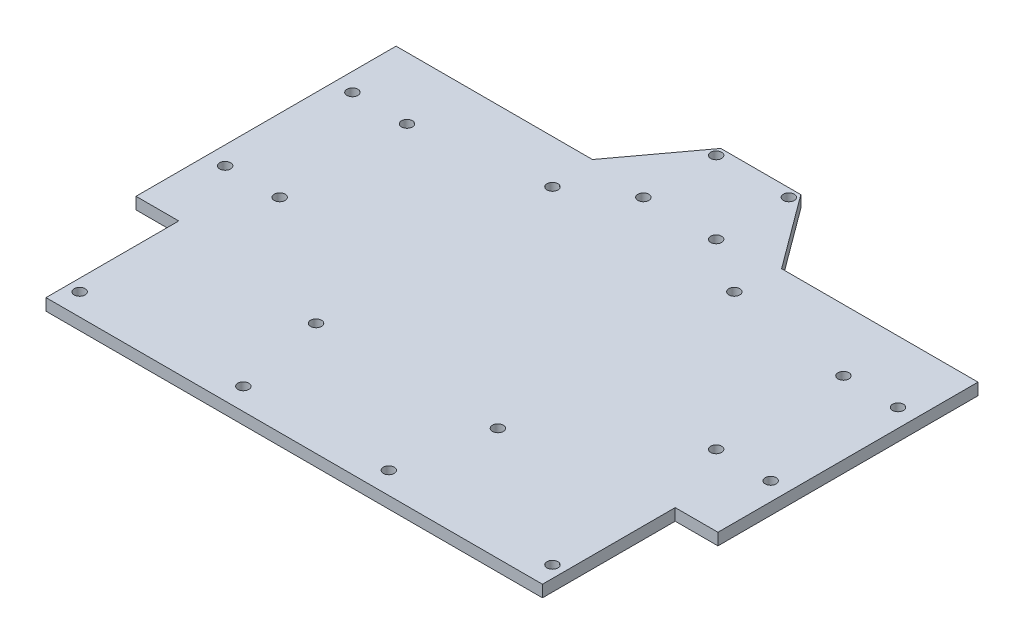
SolidWorks part; units mm, degrees
ref_plane "Front Plane" through (0, 0, 0) normal (0, 0, 1) x (1, 0, 0)
ref_plane "Top Plane" through (0, 0, 0) normal (0, 1, 0) x (1, 0, 0)
ref_plane "Right Plane" through (0, 0, 0) normal (1, 0, 0) x (0, 0, -1)
sketch "Sketch1" plane through (0, 0, 0) normal (0, 1, 0) x (1, 0, 0)
  line L1 (-11, 56.0362) -> (11, 56.0362)
  line L2 (-80, 35.75) -> (-80, -35.75)
  line L3 (-68.25, -72.25) -> (68.25, -72.25)
  line L4 (80, 35.75) -> (80, -35.75)
  line L5 (-80, -35.75) -> (-68.25, -35.75)
  line L6 (-68.25, -72.25) -> (-68.25, -35.75)
  line L7 (68.25, -72.25) -> (68.25, -35.75)
  line L8 (68.25, -35.75) -> (80, -35.75)
  line L9 (-80, 35.75) -> (-26, 35.75)
  line L10 (-26, 35.75) -> (-11, 56.0362)
  line L11 (11, 56.0362) -> (26, 35.75)
  line L12 (26, 35.75) -> (80, 35.75)
  circle A13 centre (-10, 33.75) radius 1.5025
  circle A17 centre (10, 33.75) radius 1.5025
  circle A134 centre (-10, 53.75) radius 1.5025
  circle A138 centre (10, 53.75) radius 1.5025
  circle A195 centre (-25, 23.75) radius 1.5025
  circle A205 centre (25, 23.75) radius 1.5025
  circle A218 centre (-60, 18.75) radius 1.5025
  circle A242 centre (60, 18.75) radius 1.5025
  circle A245 centre (75, 18.75) radius 1.5025
  circle A428 centre (-60, -16.25) radius 1.5025
  circle A452 centre (60, -16.25) radius 1.5025
  circle A455 centre (75, -16.25) radius 1.5025
  circle A585 centre (-25, -41.25) radius 1.5025
  circle A595 centre (25, -41.25) radius 1.5025
  circle A727 centre (-65, -66.25) radius 1.5025
  circle A736 centre (-20, -66.25) radius 1.5025
  circle A744 centre (20, -66.25) radius 1.5025
  circle A753 centre (65, -66.25) radius 1.5025
  circle A757 centre (-75, 18.75) radius 1.5025
  circle A764 centre (-75, -16.25) radius 1.5025
  dimension "D12" = 15
  dimension "D13" = 17
  dimension "D14" = 15
  dimension "D18" = 5
  dimension "D19" = 5
  dimension "D23" = 45
  dimension "D39" = 35
  dimension "D1" = 108
  dimension "D2" = 52
  dimension "D3" = 22
  dimension "D4" = 71.5
  dimension "D5" = 36.5
  dimension "D6" = 136.5
  dimension "D7" = 15
  dimension "D8" = 160
  dimension "D9" = 54
  dimension "D10" = 11.75
  dimension "D11" = 36.5
  dimension "D17" = 17
  dimension "D22" = 19.5
  dimension "D15" = 19.5
  dimension "D16" = 15
  dimension "D20" = 15
  dimension "D21" = 5
  dimension "D24" = 3.25
  dimension "D25" = 43.25
  dimension "D26" = 43.25
  dimension "D27" = 45
  dimension "D28" = 3.25
  dimension "D29" = 25
  dimension "D30" = 25
  dimension "D31" = 50
  dimension "D32" = 12
  dimension "D33" = 20
  dimension "D34" = 20
  dimension "D35" = 20
  dimension "D36" = 2.2862
  dimension "D37" = 6
  dimension "D38" = 6
extrude "Boss-Extrude1" add sketch "Sketch1" along normal blind 3.25
